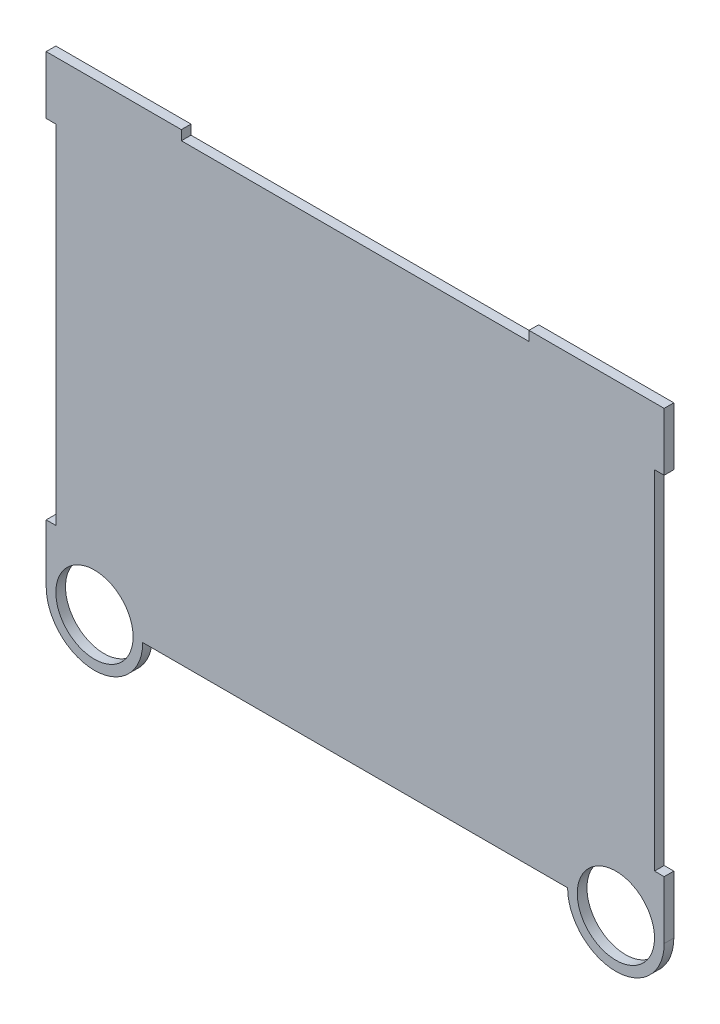
SolidWorks part; units mm, degrees
ref_plane "Front" through (0, 0, 0) normal (0, 0, 1) x (1, 0, 0)
ref_plane "Top" through (0, 0, 0) normal (0, 1, 0) x (1, 0, 0)
ref_plane "Right" through (0, 0, 0) normal (1, 0, 0) x (0, 0, -1)
sketch "Sketch1" plane through (0, 0, 0) normal (0, 0, 1) x (1, 0, 0)
  line L2 (0, 0) -> (0, 152.4)
  line L3 (0, 152.4) -> (203.2, 152.4)
  line L4 (203.2, 0) -> (203.2, 152.4)
  line L9 (31.75, 0) -> (171.45, 0)
  arc A0 (0, 0) -> (31.75, 0) centre (15.875, 0) ccw
  arc A1 (171.45, 0) -> (203.2, 0) centre (187.325, 0) ccw
  dimension "D3" = 31.75
  dimension "D1" = 152.4
  dimension "D2" = 203.2
extrude "Boss-Extrude1" add sketch "Sketch1" along normal blind 3.175
sketch "Sketch2" plane through (0, 0, 3.175) normal (0, 0, 1) x (1, 0, 0)
  circle A4 centre (15.875, 0) radius 12.7
  circle A5 centre (187.325, 0) radius 12.7
  dimension "D1" = 25.4
extrude "Cut-Extrude1" cut sketch "Sketch2" against normal through all and the other way through all
sketch "Sketch3" plane through (0, 0, 3.175) normal (0, 0, 1) x (1, 0, 0)
  line L0 (203.2, 0) -> (203.2, 152.4) construction
  line L1 (203.2, 19.05) -> (200.025, 19.05)
  line L2 (203.2, 19.05) -> (203.2, 133.35)
  line L3 (203.2, 133.35) -> (200.025, 133.35)
  line L4 (200.025, 19.05) -> (200.025, 133.35)
  line L5 (0, 152.4) -> (0, 0) construction
  line L6 (0, 19.05) -> (3.175, 19.05)
  line L7 (0, 19.05) -> (0, 133.35)
  line L8 (0, 133.35) -> (3.175, 133.35)
  line L9 (3.175, 19.05) -> (3.175, 133.35)
  line L10 (203.2, 152.4) -> (0, 152.4) construction
  line L11 (203.2, 152.4) -> (0, 152.4) construction
  line L14 (158.75, 152.4) -> (44.45, 152.4)
  line L15 (158.75, 152.4) -> (158.75, 149.225)
  line L16 (158.75, 149.225) -> (44.45, 149.225)
  line L17 (44.45, 152.4) -> (44.45, 149.225)
  dimension "D1" = 19.05
  dimension "D2" = 19.05
  dimension "D3" = 114.3
  dimension "D4" = 114.3
  dimension "D5" = 44.45
  dimension "D6" = 3.175
  dimension "D7" = 3.175
extrude "Cut-Extrude2" cut sketch "Sketch3" against normal through all
